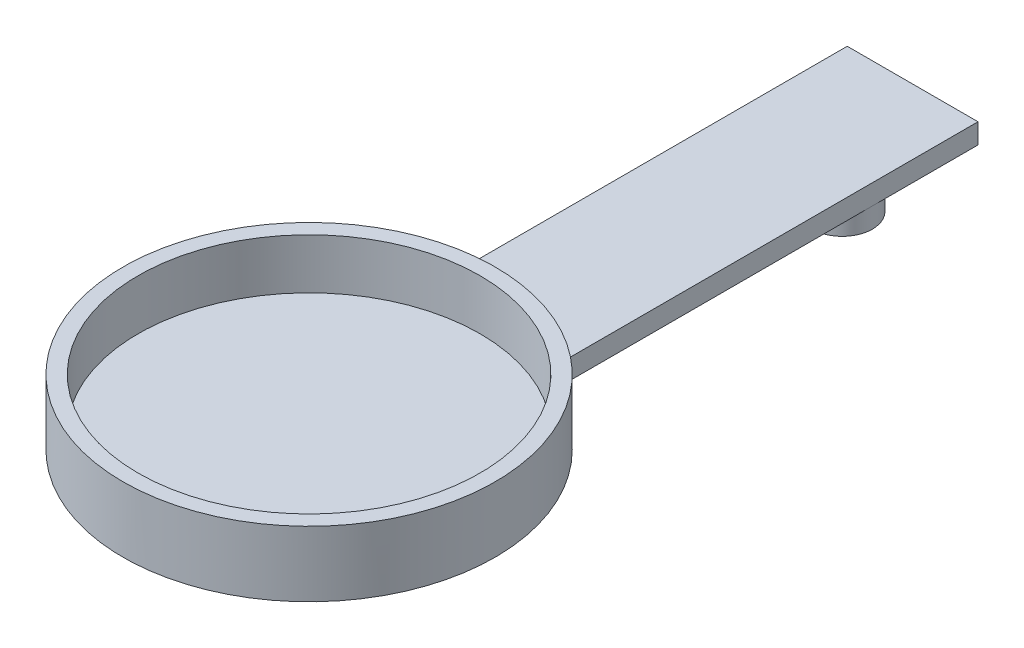
SolidWorks part; units mm, degrees
ref_plane "Front Plane" through (0, 0, 0) normal (0, 0, 1) x (1, 0, 0)
ref_plane "Top Plane" through (0, 0, 0) normal (0, 1, 0) x (1, 0, 0)
ref_plane "Right Plane" through (0, 0, 0) normal (1, 0, 0) x (0, 0, -1)
sketch "Sketch1" plane through (0, 0, 0) normal (0, 1, 0) x (1, 0, 0)
  circle A0 centre (0, 0) radius 18.5
extrude "Boss-Extrude1" add sketch "Sketch1" along normal blind 1.5
sketch "Sketch2" plane through (0, 1.5, 0) normal (0, 1, 0) x (1, 0, 0)
  circle A0 centre (0, 0) radius 17
  circle A1 centre (0, 0) radius 18.5
extrude "Boss-Extrude2" add sketch "Sketch2" along normal blind 5
sketch "Sketch3" plane through (0, 0, 0) normal (0, -1, 0) x (-1, 0, 0)
  line L0 (6.5, 60) -> (-6.5, 60)
  line L1 (6.5, 60) -> (6.5, -11.1087)
  line L2 (-6.5, 60) -> (-6.5, -11.1087)
  line L3 (6.5, -11.1087) -> (-6.5, -11.1087)
  point P0 (0, 60)
  point P1 (6.5, 60)
  point P2 (-6.5, 60)
  point P3 (0, -11)
  point P7 (-6.5, -11)
  dimension "D1" = 11
  dimension "D2" = 60
  dimension "D3" = 6.5
  dimension "D4" = 6.5
extrude "Boss-Extrude3" add sketch "Sketch3" along normal blind 0.5 and the other way blind 1.5
sketch "Sketch4" plane through (0, -0.5, 0) normal (0, -1, 0) x (-1, 0, 0)
  line L0 (-6.5, -11.1087) -> (6.5, -11.1087) construction
  line L1 (6.5, 60) -> (-6.5, 60) construction
  circle A0 centre (3.5, -9.1087) radius 3
  circle A1 centre (-3.5, 49.5) radius 3
  circle A2 centre (-3.5, -9.1087) radius 3
  point P0 (3.5, -11.1087)
  point P1 (3.5, -9.1087)
  point P7 (-3.5, 60)
  point P8 (-3.5, 49.5)
  point P14 (-3.5, -9.1087)
  dimension "D3" = 3
  dimension "D1" = 3
  dimension "D2" = 2
  dimension "D4" = 10.5
extrude "Boss-Extrude4" add sketch "Sketch4" along normal blind 2 and the other way blind 0.5
sketch "Sketch6" plane through (0, -2.5, 0) normal (0, -1, 0) x (-1, 0, 0)
  line L0 (-3.5, 51.5) -> (-3.5, 52.5)
  line L1 (-3.5, 46.5) -> (-3.5, 47.5)
  arc A0 (-3.5, 51.5) -> (-3.5, 47.5) centre (-3.5, 49.5) cw
  circle A1 centre (-3.5, 49.5) radius 3 construction
  arc A2 (-3.5, 46.5) -> (-3.5, 52.5) centre (-3.5, 49.5) ccw
  point P0 (-3.5, 49.5)
  point P1 (-3.5, 51.5)
  point P3 (-3.5, 47.5)
  dimension "D1" = 2
  dimension "D2" = 2
extrude "Cut-Extrude1" cut sketch "Sketch6" against normal blind 2
sketch "Sketch7" plane through (0, -2.5, 0) normal (0, -1, 0) x (-1, 0, 0)
  arc A0 (-3.5, 47.5) -> (-3.5, 51.5) centre (-3.5, 49.5) ccw construction
  circle A1 centre (-3.5, 49.5) radius 1.4
  circle A2 centre (3.5, -9.1087) radius 1.4
  point P0 (-1.5, 49.5)
  point P1 (-3.5, 49.5)
  point P7 (3.5, -9.1087)
  dimension "D1" = 2
extrude "Cut-Extrude2" cut sketch "Sketch7" against normal blind 3
